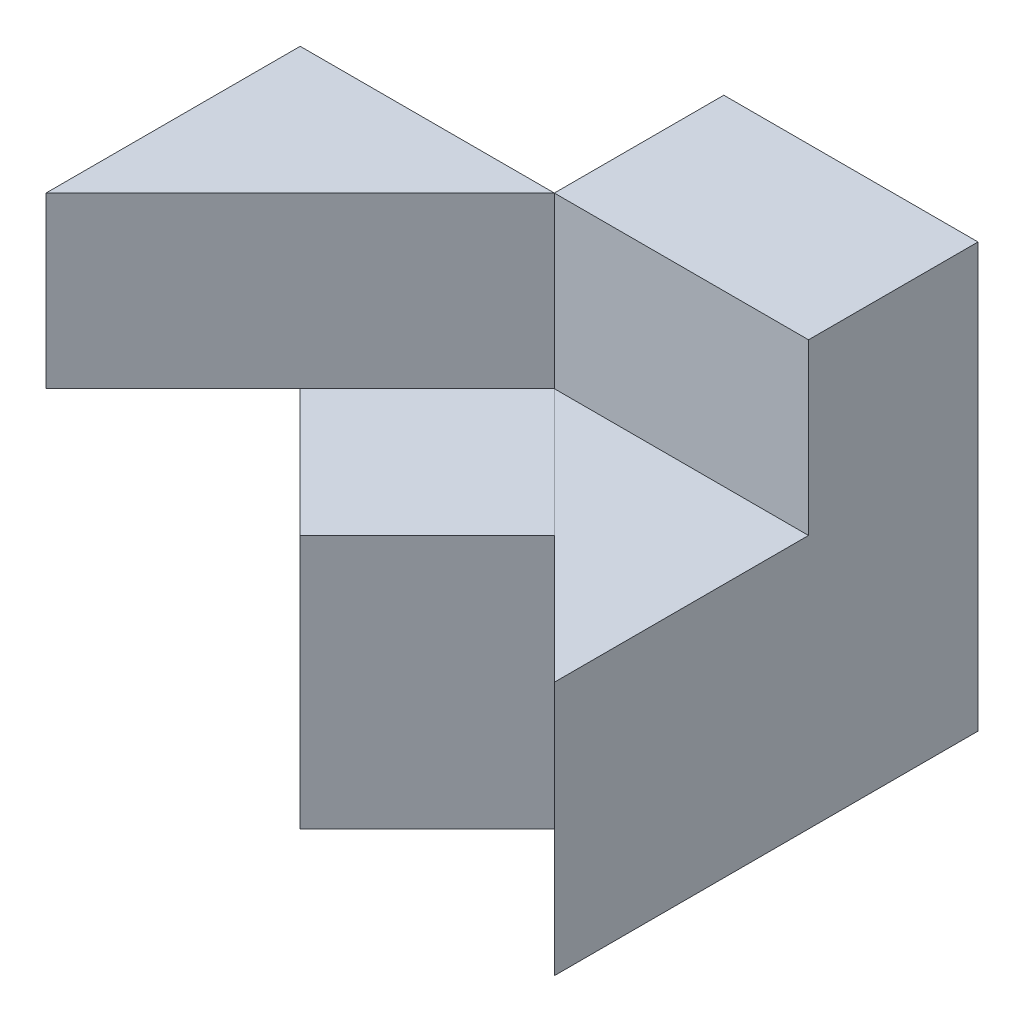
SolidWorks part; units mm, degrees
ref_plane "Front Plane" through (0, 0, 0) normal (0, 0, 1) x (1, 0, 0)
ref_plane "Top Plane" through (0, 0, 0) normal (0, 1, 0) x (1, 0, 0)
ref_plane "Right Plane" through (0, 0, 0) normal (1, 0, 0) x (0, 0, -1)
sketch "Sketch1" plane through (0, 0, 0) normal (0, 0, 1) x (1, 0, 0)
  line L1 (0, 0) -> (60, 0)
  line L2 (0, 0) -> (0, 50)
  line L3 (0, 50) -> (60, 50)
  line L4 (60, 0) -> (60, 50)
  dimension "D1" = 60
  dimension "D2" = 50
extrude "Boss-Extrude1" add sketch "Sketch1" along normal blind 50
sketch "Sketch2" plane through (0, 50, 0) normal (0, 1, 0) x (1, 0, 0)
  line L1 (0, 0) -> (30, 0)
  line L2 (0, 0) -> (0, -20)
  line L3 (0, -20) -> (30, -20)
  line L4 (30, 0) -> (30, -20)
  dimension "D1" = 30
  dimension "D2" = 20
extrude "Cut-Extrude1" cut sketch "Sketch2" against normal blind 50
sketch "Sketch3" plane through (0, 50, 0) normal (0, 1, 0) x (1, 0, 0)
  line L0 (0, -50) -> (15, -35)
  line L1 (15, -35) -> (30, -50)
  line L2 (60, -50) -> (0, -50) construction
  line L3 (30, -50) -> (45, -35)
  line L4 (45, -35) -> (60, -50)
  line L5 (60, -50) -> (60, 0) construction
  line L6 (0, -50) -> (60, -50)
  line M5 (0, -50) -> (60, -50)
  dimension "D1" = 15
  dimension "D2" = 15
  dimension "D3" = 15
  dimension "D4" = 15
  dimension "D5" = 15
extrude "Cut-Extrude2" cut sketch "Sketch3" against normal blind 50 contours L1 L0 M5 | L4 L3 M5
ref_plane "Plane1" through (0, 0, 50) normal (0, 0, 1) x (1, 0, 0)
sketch "Sketch5" plane through (0, 0, 50) normal (0, 0, 1) x (1, 0, 0)
  line L0 (30, 0) -> (30, 50) construction
  line L1 (60, 50) -> (30, 50)
  line L2 (60, 50) -> (60, 30)
  line L3 (60, 30) -> (30, 30)
  line L4 (30, 50) -> (30, 30)
  dimension "D1" = 20
extrude "Cut-Extrude6" cut sketch "Sketch5" against normal blind 29.999
ref_plane "Plane2" through (0, 0, 50) normal (0, 0, 1) x (1, 0, 0)
sketch "Sketch7" plane through (0, 0, 50) normal (0, 0, 1) x (1, 0, 0)
  line L1 (0, 0) -> (29.999, 0)
  line L2 (0, 0) -> (0, 29.999)
  line L3 (0, 29.999) -> (29.999, 29.999)
  line L4 (29.999, 0) -> (29.999, 29.999)
  dimension "D1" = 29.999
  dimension "D2" = 29.999
extrude "Cut-Extrude10" cut sketch "Sketch7" against normal blind 29.999
ref_plane "Plane3" through (0, 50, 0) normal (0, 1, 0) x (1, 0, 0)
sketch "Sketch8" plane through (0, 50, 0) normal (0, 1, 0) x (1, 0, 0)
  line L0 (15, -35) -> (30, -20.001)
  line L1 (30, -20.001) -> (44.999, -35.001)
  line L2 (44.999, -35.001) -> (30, -50)
  line L3 (15, -35) -> (30, -50) construction
  line L4 (30, -20.001) -> (30, -50) construction
  line L5 (30, -50) -> (15, -35)
extrude "Cut-Extrude11" cut sketch "Sketch8" against normal blind 20
sketch "Sketch11" plane through (0, 50, 0) normal (0, 1, 0) x (1, 0, 0)
  line L0 (0, -50) -> (0, -20)
  line L1 (0, -20) -> (30, -20.001)
  line L2 (30, -20.001) -> (0, -50)
extrude "Boss-Extrude5" add sketch "Sketch11" against normal blind 20
sketch "Sketch14" plane through (0, 29.999, 0) normal (0, -1, 0) x (-1, 0, 0)
  line L0 (-15, -35) -> (0, -20.001)
  line L1 (0, -20.001) -> (-29.999, -20.001)
  line L2 (-29.999, -20.001) -> (-15, -35)
  line L3 (-15, -35) -> (0, -50)
  line L4 (0, -50) -> (0, -20.001)
  line M2 (-15, -35) -> (0, -50)
  line M3 (0, -50) -> (0, -20.001)
extrude "Cut-Extrude17" cut sketch "Sketch14" against normal blind 0.0001 contours L0 M2 M3
sketch "Sketch15" plane through (0, 0, 0) normal (0, -1, 0) x (-1, 0, 0)
  line L0 (-45, -35) -> (-60, -20)
  line L1 (-60, -50) -> (-60, 0) construction
  line L2 (-60, -20) -> (-60, -50)
  line L3 (-60, -50) -> (-45, -35)
extrude "Cut-Extrude18" cut sketch "Sketch15" against normal blind 0.0001
sketch "Sketch16" plane through (0, 30, 0) normal (0, 1, 0) x (1, 0, 0)
  line L0 (45, -35) -> (30, -20.001)
  line L1 (30, -20.001) -> (15.0003, -35.0003)
  line L3 (30, -50) -> (45, -35)
  line L9 (60, -20.001) -> (30, -20.001)
  line L10 (30, -20.001) -> (15.0003, -35.0003)
  line L11 (15.0003, -35.0003) -> (30, -50)
  line L12 (30, -50) -> (45, -35)
  line L13 (45, -35) -> (60, -50)
  line L14 (60, -50) -> (60, -20.001)
  line L15 (60, -20.001) -> (30, -20.001)
  line L16 (30, -20.001) -> (15.0003, -35.0003)
  line L18 (30, -50) -> (45, -35)
  line L19 (45, -35) -> (60, -50)
  line L20 (60, -50) -> (60, -20.001)
  line M8 (30, -20.001) -> (15.0003, -35.0003)
  line M9 (15.0003, -35.0003) -> (30, -50)
  line M10 (30, -50) -> (45, -35)
  dimension "D1" = 0
extrude "Boss-Extrude16" add sketch "Sketch16" along normal blind 0.0001 contours L0 M10 M8 M9
